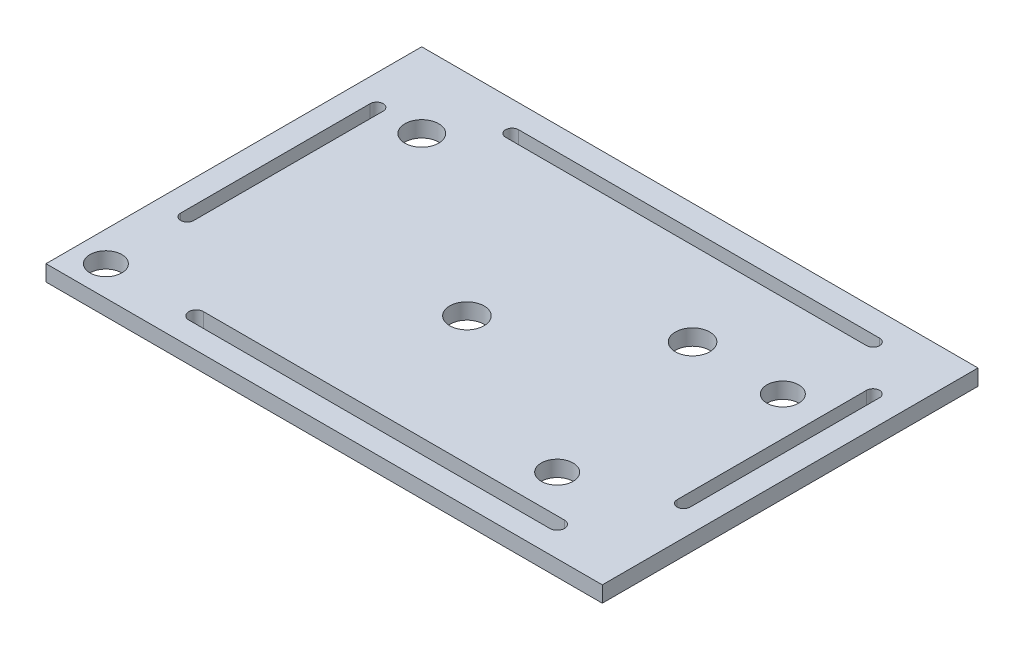
SolidWorks part; units mm, degrees
ref_plane "Front Plane" through (0, 0, 0) normal (0, 0, 1) x (1, 0, 0)
ref_plane "Top Plane" through (0, 0, 0) normal (0, 1, 0) x (1, 0, 0)
ref_plane "Right Plane" through (0, 0, 0) normal (1, 0, 0) x (0, 0, -1)
sketch "Sketch1" plane through (0, 0, 0) normal (0, 1, 0) x (1, 0, 0)
  line L1 (27.4816, -38.3581) -> (-83.4547, -38.3581)
  line L2 (27.4816, -38.3581) -> (27.4816, 36.561)
  line L3 (27.4816, 36.561) -> (-83.4547, 36.561)
  line L4 (-83.4547, -38.3581) -> (-83.4547, 36.561)
  line L5 (27.4816, -36.0725) -> (27.4816, -1.2741) construction
  line L6 (25.196, 36.561) -> (-81.1691, 36.561) construction
  line L7 (-81.1691, -38.3581) -> (25.196, -38.3581) construction
  line L8 (-83.4547, 34.2753) -> (-83.4547, -36.0725) construction
  point P0 (0, 0)
extrude "Boss-Extrude1" add sketch "Sketch1" along normal blind 3.175
sketch "Sketch2" plane through (0, 0, 0) normal (0, -1, 0) x (1, 0, 0)
  circle A3 centre (-77.4734, 32.3946) radius 3.175
  dimension "D2" = 6.35
extrude "Cut-Extrude1" cut sketch "Sketch2" against normal through all
sketch "Sketch7" plane through (0, 3.175, 0) normal (0, 1, 0) x (1, 0, 0)
  line L0 (-83.4547, -0.8986) -> (27.4816, -0.8986) construction
  line L1 (-83.4547, 36.561) -> (-83.4547, -38.3581) construction
  line L2 (27.4816, -38.3581) -> (27.4816, 36.561) construction
sketch "Sketch8" plane through (0, 3.175, 0) normal (0, 1, 0) x (1, 0, 0)
sketch "Sketch10" plane through (0, 3.175, 0) normal (0, 1, 0) x (1, 0, 0)
  circle A1 centre (3.5196, -23.3954) radius 3.175
  circle A2 centre (12.5188, 12.6015) radius 3.175
  dimension "D1" = 6.35
  dimension "D2" = 6.35
extrude "Cut-Extrude5" cut sketch "Sketch10" against normal through all
sketch "Sketch11" plane through (0, 3.175, 0) normal (0, 1, 0) x (1, 0, 0)
  line L0 (-77.4734, -16.1754) -> (-77.4734, 21.6007) construction
  line L1 (-78.7704, -16.1754) -> (-78.7704, 21.6007)
  line L2 (-76.1763, -16.1754) -> (-76.1763, 21.6007)
  line L3 (-59.4749, 30.6) -> (12.5188, 30.6) construction
  line L4 (-59.4749, 31.8993) -> (12.5188, 31.8993)
  line L5 (-59.4749, 29.3006) -> (12.5188, 29.3006)
  line L6 (12.5188, -32.3946) -> (-59.4749, -32.3946) construction
  line L7 (12.5188, -33.8525) -> (-59.4749, -33.8525)
  line L8 (12.5188, -30.9366) -> (-59.4749, -30.9366)
  line L9 (21.518, -16.1754) -> (21.518, 21.6007) construction
  line L10 (20.2264, -16.1754) -> (20.2264, 21.6007)
  line L11 (22.8097, -16.1754) -> (22.8097, 21.6007)
  arc A0 (-78.7704, -16.1754) -> (-76.1763, -16.1754) centre (-77.4734, -16.1754) ccw
  arc A1 (-76.1763, 21.6007) -> (-78.7704, 21.6007) centre (-77.4734, 21.6007) ccw
  arc A2 (-59.4749, 31.8993) -> (-59.4749, 29.3006) centre (-59.4749, 30.6) ccw
  arc A3 (12.5188, 29.3006) -> (12.5188, 31.8993) centre (12.5188, 30.6) ccw
  arc A4 (12.5188, -33.8525) -> (12.5188, -30.9366) centre (12.5188, -32.3946) ccw
  arc A5 (-59.4749, -30.9366) -> (-59.4749, -33.8525) centre (-59.4749, -32.3946) ccw
  arc A6 (20.2264, -16.1754) -> (22.8097, -16.1754) centre (21.518, -16.1754) ccw
  arc A7 (22.8097, 21.6007) -> (20.2264, 21.6007) centre (21.518, 21.6007) ccw
  point P4 (-77.4734, 2.7127)
  point P9 (-23.4781, 30.6)
  point P18 (-23.4781, -32.3946)
  point P27 (21.518, 2.7127)
extrude "Cut-Extrude6" cut sketch "Sketch11" against normal through all
sketch "Sketch12" plane through (0, 3.175, 0) normal (0, 1, 0) x (1, 0, 0)
  circle A0 centre (-68.4742, 21.6007) radius 3.3701
  circle A1 centre (-32.4773, -5.3969) radius 3.429
  circle A2 centre (-5.4796, 12.6015) radius 3.429
  dimension "D1" = 6.7402
  dimension "D2" = 6.858
  dimension "D3" = 6.858
extrude "Cut-Extrude7" cut sketch "Sketch12" against normal through all
